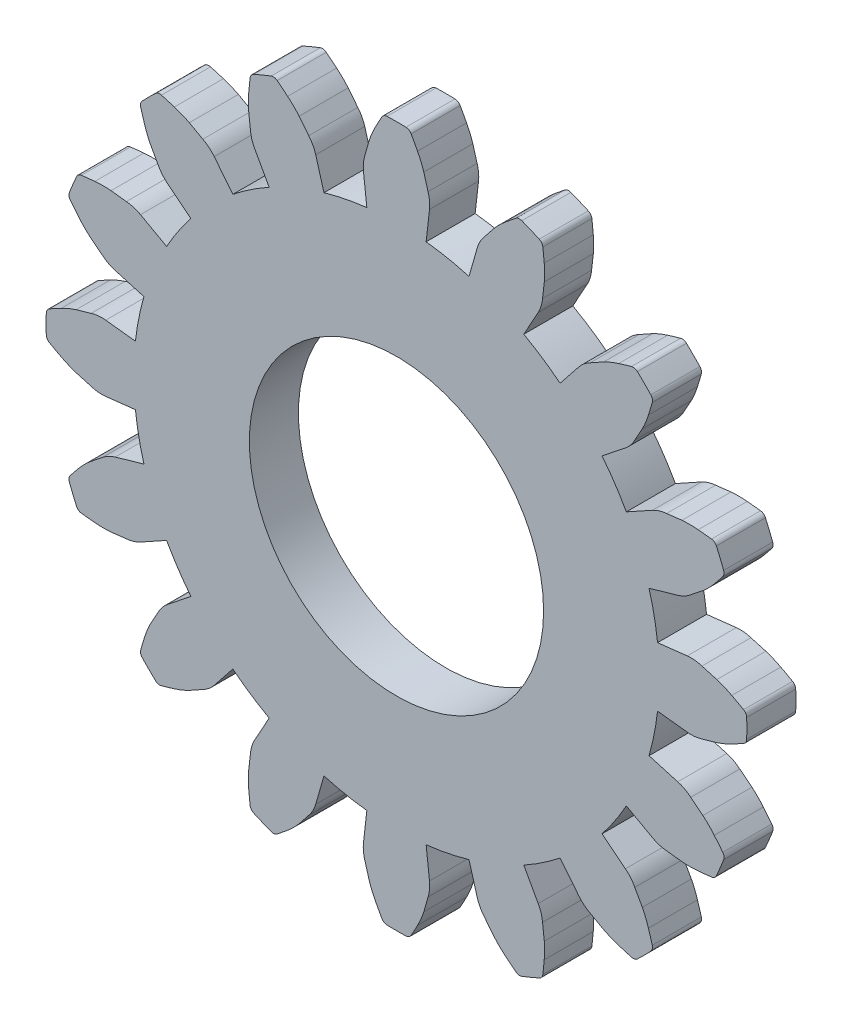
SolidWorks part; units mm, degrees
ref_plane "Front Plane" through (0, 0, 0) normal (0, 0, 1) x (1, 0, 0)
ref_plane "Top Plane" through (0, 0, 0) normal (0, 1, 0) x (1, 0, 0)
ref_plane "Right Plane" through (0, 0, 0) normal (1, 0, 0) x (0, 0, -1)
sketch "Model" plane through (0, 0, 0) normal (0, 0, 1) x (1, 0, 0)
  line L0 (26.7827, 18.0118) -> (27.9934, 18.1493)
  line L1 (26.7827, 15.5936) -> (27.9934, 15.4561)
  line L2 (26.435, 13.8453) -> (27.6061, 13.509)
  line L3 (25.5095, 11.6111) -> (26.5755, 11.0208)
  line L4 (24.5192, 10.129) -> (25.4725, 9.3701)
  line L5 (22.8092, 8.419) -> (23.5681, 7.4657)
  line L6 (21.3271, 7.4287) -> (21.9175, 6.3628)
  line L7 (19.0929, 6.5033) -> (19.4292, 5.3321)
  line L8 (17.3447, 6.1555) -> (17.4822, 4.9448)
  line L9 (14.9264, 6.1555) -> (14.7889, 4.9448)
  line L10 (13.1781, 6.5033) -> (12.8418, 5.3321)
  line L11 (10.9439, 7.4287) -> (10.3536, 6.3628)
  line L12 (9.4618, 8.419) -> (8.703, 7.4657)
  line L13 (7.7518, 10.129) -> (6.7985, 9.3701)
  line L14 (6.7615, 11.6111) -> (5.6956, 11.0208)
  line L15 (5.8361, 13.8453) -> (4.665, 13.509)
  line L16 (5.4883, 15.5936) -> (4.2777, 15.4561)
  line L17 (5.4883, 18.0118) -> (4.2777, 18.1493)
  line L18 (5.8361, 19.7601) -> (4.665, 20.0964)
  line L19 (6.7615, 21.9943) -> (5.6956, 22.5846)
  line L20 (7.7518, 23.4764) -> (6.7985, 24.2353)
  line L21 (9.4618, 25.1864) -> (8.703, 26.1397)
  line L22 (10.9439, 26.1767) -> (10.3536, 27.2426)
  line L23 (13.1781, 27.1021) -> (12.8418, 28.2733)
  line L24 (14.9264, 27.4499) -> (14.7889, 28.6606)
  line L25 (17.3447, 27.4499) -> (17.4822, 28.6606)
  line L26 (19.0929, 27.1021) -> (19.4292, 28.2733)
  line L27 (21.3271, 26.1767) -> (21.9175, 27.2426)
  line L28 (22.8092, 25.1864) -> (23.5681, 26.1397)
  line L29 (24.5192, 23.4764) -> (25.4725, 24.2353)
  line L30 (25.5095, 21.9943) -> (26.5755, 22.5846)
  line L31 (26.435, 19.7601) -> (27.6061, 20.0964)
  arc A0 (26.7827, 18.0118) -> (26.6453, 18.8932) centre (16.1355, 16.8027) ccw
  arc A1 (28.5916, 18.09) -> (27.9934, 18.1493) centre (28.1546, 16.7294) ccw
  arc A2 (29.1989, 17.9171) -> (28.5916, 18.09) centre (-551.5526, -2020.9533) ccw
  arc A3 (29.8078, 17.661) -> (29.1989, 17.9171) centre (28.0353, 14.2986) ccw
  arc A4 (30.2897, 17.4001) -> (29.8078, 17.661) centre (18.6277, -3.5692) ccw
  arc A5 (30.423, 16.8027) -> (30.4178, 17.189) centre (16.1355, 16.8027) ccw
  arc A6 (30.4178, 17.189) -> (30.2897, 17.4001) centre (30.1685, 17.1822) ccw
  arc A7 (26.6453, 14.7122) -> (26.7827, 15.5936) centre (16.1355, 16.8027) ccw
  arc A8 (27.9934, 15.4561) -> (28.5916, 15.5154) centre (28.1546, 16.876) ccw
  arc A9 (28.5916, 15.5154) -> (29.1989, 15.6883) centre (-551.5526, 2054.5587) ccw
  arc A10 (29.1989, 15.6883) -> (29.8078, 15.9444) centre (28.0353, 19.3068) ccw
  arc A11 (29.8078, 15.9444) -> (30.2897, 16.2052) centre (18.6277, 37.1746) ccw
  arc A12 (30.4178, 16.4164) -> (30.423, 16.8027) centre (16.1355, 16.8027) ccw
  arc A13 (30.2897, 16.2052) -> (30.4178, 16.4164) centre (30.1685, 16.4232) ccw
  arc A14 (26.435, 13.8453) -> (26.6453, 14.7122) centre (16.1355, 16.8027) ccw
  arc A15 (28.1361, 13.2252) -> (27.6061, 13.509) centre (27.2117, 12.1355) ccw
  arc A16 (28.631, 12.8332) -> (28.1361, 13.2252) centre (-1288.1554, -1648.5936) ccw
  arc A17 (29.0955, 12.3636) -> (28.631, 12.8332) centre (26.1712, 9.9353) ccw
  arc A18 (29.441, 11.9381) -> (29.0955, 12.3636) centre (10.642, -2.9722) ccw
  arc A19 (29.3355, 11.3351) -> (29.4785, 11.694) centre (16.1355, 16.8027) ccw
  arc A20 (29.4785, 11.694) -> (29.441, 11.9381) centre (29.2456, 11.7831) ccw
  arc A21 (25.0453, 10.8494) -> (25.5095, 11.6111) centre (16.1355, 16.8027) ccw
  arc A22 (26.5755, 11.0208) -> (27.1509, 10.8466) centre (27.2678, 12.2709) ccw
  arc A23 (27.1509, 10.8466) -> (27.778, 10.774) centre (271.4756, 2116.6886) ccw
  arc A24 (27.778, 10.774) -> (28.4386, 10.7776) centre (28.0878, 14.5623) ccw
  arc A25 (28.4386, 10.7776) -> (28.9837, 10.8341) centre (26.234, 34.6702) ccw
  arc A26 (29.1828, 10.9802) -> (29.3355, 11.3351) centre (16.1355, 16.8027) ccw
  arc A27 (28.9837, 10.8341) -> (29.1828, 10.9802) centre (28.9551, 11.0819) ccw
  arc A28 (24.5192, 10.129) -> (25.0453, 10.8494) centre (16.1355, 16.8027) ccw
  arc A29 (25.8536, 8.9051) -> (25.4725, 9.3701) centre (24.5825, 8.2521) ccw
  arc A30 (26.1607, 8.3535) -> (25.8536, 8.9051) centre (-1826.1917, -1022.6923) ccw
  arc A31 (26.4102, 7.7419) -> (26.1607, 8.3535) centre (22.7793, 6.6176) ccw
  arc A32 (26.5665, 7.2166) -> (26.4102, 7.7419) centre (3.4927, 0.6353) ccw
  arc A33 (26.2383, 6.6999) -> (26.5078, 6.9767) centre (16.1355, 16.8027) ccw
  arc A34 (26.5078, 6.9767) -> (26.5665, 7.2166) centre (26.3267, 7.1482) ccw
  arc A35 (22.0888, 7.893) -> (22.8092, 8.419) centre (16.1355, 16.8027) ccw
  arc A36 (23.5681, 7.4657) -> (24.0331, 7.0846) centre (24.6862, 8.3557) ccw
  arc A37 (24.0331, 7.0846) -> (24.5847, 6.7775) centre (1055.6305, 1859.1299) ccw
  arc A38 (24.5847, 6.7775) -> (25.1963, 6.528) centre (26.3206, 10.159) ccw
  arc A39 (25.1963, 6.528) -> (25.7216, 6.3717) centre (32.3029, 29.4456) ccw
  arc A40 (25.9615, 6.4305) -> (26.2383, 6.6999) centre (16.1355, 16.8027) ccw
  arc A41 (25.7216, 6.3717) -> (25.9615, 6.4305) centre (25.79, 6.6115) ccw
  arc A42 (21.3271, 7.4287) -> (22.0888, 7.893) centre (16.1355, 16.8027) ccw
  arc A43 (22.0916, 5.7874) -> (21.9175, 6.3628) centre (20.6673, 5.6704) ccw
  arc A44 (22.1643, 5.1602) -> (22.0916, 5.7874) centre (-2083.7504, -238.5374) ccw
  arc A45 (22.1607, 4.4997) -> (22.1643, 5.1602) centre (18.3759, 4.8504) ccw
  arc A46 (22.1041, 3.9545) -> (22.1607, 4.4997) centre (-1.7319, 6.7042) ccw
  arc A47 (21.6031, 3.6028) -> (21.958, 3.7554) centre (16.1355, 16.8027) ccw
  arc A48 (21.958, 3.7554) -> (22.1041, 3.9545) centre (21.8564, 3.9831) ccw
  arc A49 (18.226, 6.293) -> (19.0929, 6.5033) centre (16.1355, 16.8027) ccw
  arc A50 (19.4292, 5.3321) -> (19.713, 4.8021) centre (20.8028, 5.7265) ccw
  arc A51 (19.713, 4.8021) -> (20.1051, 4.3073) centre (1681.5318, 1321.0936) ccw
  arc A52 (20.1051, 4.3073) -> (20.5747, 3.8427) centre (23.0029, 6.767) ccw
  arc A53 (20.5747, 3.8427) -> (21.0001, 3.4973) centre (35.9105, 22.2962) ccw
  arc A54 (21.2443, 3.4598) -> (21.6031, 3.6028) centre (16.1355, 16.8027) ccw
  arc A55 (21.0001, 3.4973) -> (21.2443, 3.4598) centre (21.1551, 3.6926) ccw
  arc A56 (17.3447, 6.1555) -> (18.226, 6.293) centre (16.1355, 16.8027) ccw
  arc A57 (17.4228, 4.3466) -> (17.4822, 4.9448) centre (16.0622, 4.7836) ccw
  arc A58 (17.25, 3.7393) -> (17.4228, 4.3466) centre (-2021.6205, 584.4908) ccw
  arc A59 (16.9939, 3.1305) -> (17.25, 3.7393) centre (13.6314, 4.9029) ccw
  arc A60 (16.733, 2.6485) -> (16.9939, 3.1305) centre (-4.2364, 14.3105) ccw
  arc A61 (16.1355, 2.5152) -> (16.5218, 2.5204) centre (16.1355, 16.8027) ccw
  arc A62 (16.5218, 2.5204) -> (16.733, 2.6485) centre (16.5151, 2.7697) ccw
  arc A63 (14.045, 6.293) -> (14.9264, 6.1555) centre (16.1355, 16.8027) ccw
  arc A64 (14.7889, 4.9448) -> (14.8482, 4.3466) centre (16.2088, 4.7836) ccw
  arc A65 (14.8482, 4.3466) -> (15.0211, 3.7393) centre (2053.8916, 584.4908) ccw
  arc A66 (15.0211, 3.7393) -> (15.2772, 3.1305) centre (18.6397, 4.9029) ccw
  arc A67 (15.2772, 3.1305) -> (15.5381, 2.6485) centre (36.5075, 14.3105) ccw
  arc A68 (15.7493, 2.5204) -> (16.1355, 2.5152) centre (16.1355, 16.8027) ccw
  arc A69 (15.5381, 2.6485) -> (15.7493, 2.5204) centre (15.756, 2.7697) ccw
  arc A70 (13.1781, 6.5033) -> (14.045, 6.293) centre (16.1355, 16.8027) ccw
  arc A71 (12.5581, 4.8021) -> (12.8418, 5.3321) centre (11.4683, 5.7265) ccw
  arc A72 (12.166, 4.3073) -> (12.5581, 4.8021) centre (-1649.2607, 1321.0936) ccw
  arc A73 (11.6964, 3.8427) -> (12.166, 4.3073) centre (9.2682, 6.767) ccw
  arc A74 (11.2709, 3.4973) -> (11.6964, 3.8427) centre (-3.6394, 22.2962) ccw
  arc A75 (10.6679, 3.6028) -> (11.0268, 3.4598) centre (16.1355, 16.8027) ccw
  arc A76 (11.0268, 3.4598) -> (11.2709, 3.4973) centre (11.116, 3.6926) ccw
  arc A77 (10.1823, 7.893) -> (10.9439, 7.4287) centre (16.1355, 16.8027) ccw
  arc A78 (10.3536, 6.3628) -> (10.1795, 5.7874) centre (11.6038, 5.6704) ccw
  arc A79 (10.1795, 5.7874) -> (10.1068, 5.1602) centre (2116.0215, -238.5374) ccw
  arc A80 (10.1068, 5.1602) -> (10.1104, 4.4997) centre (13.8952, 4.8504) ccw
  arc A81 (10.1104, 4.4997) -> (10.167, 3.9545) centre (34.003, 6.7042) ccw
  arc A82 (10.3131, 3.7554) -> (10.6679, 3.6028) centre (16.1355, 16.8027) ccw
  arc A83 (10.167, 3.9545) -> (10.3131, 3.7554) centre (10.4147, 3.9831) ccw
  arc A84 (9.4618, 8.419) -> (10.1823, 7.893) centre (16.1355, 16.8027) ccw
  arc A85 (8.238, 7.0846) -> (8.703, 7.4657) centre (7.5849, 8.3557) ccw
  arc A86 (7.6864, 6.7775) -> (8.238, 7.0846) centre (-1023.3595, 1859.1299) ccw
  arc A87 (7.0747, 6.528) -> (7.6864, 6.7775) centre (5.9504, 10.159) ccw
  arc A88 (6.5495, 6.3717) -> (7.0747, 6.528) centre (-0.0318, 29.4456) ccw
  arc A89 (6.0327, 6.6999) -> (6.3096, 6.4305) centre (16.1355, 16.8027) ccw
  arc A90 (6.3096, 6.4305) -> (6.5495, 6.3717) centre (6.4811, 6.6115) ccw
  arc A91 (7.2258, 10.8494) -> (7.7518, 10.129) centre (16.1355, 16.8027) ccw
  arc A92 (6.7985, 9.3701) -> (6.4175, 8.9051) centre (7.6886, 8.2521) ccw
  arc A93 (6.4175, 8.9051) -> (6.1103, 8.3535) centre (1858.4628, -1022.6923) ccw
  arc A94 (6.1103, 8.3535) -> (5.8609, 7.7419) centre (9.4918, 6.6176) ccw
  arc A95 (5.8609, 7.7419) -> (5.7045, 7.2166) centre (28.7784, 0.6353) ccw
  arc A96 (5.7633, 6.9767) -> (6.0327, 6.6999) centre (16.1355, 16.8027) ccw
  arc A97 (5.7045, 7.2166) -> (5.7633, 6.9767) centre (5.9443, 7.1482) ccw
  arc A98 (6.7615, 11.6111) -> (7.2258, 10.8494) centre (16.1355, 16.8027) ccw
  arc A99 (5.1202, 10.8466) -> (5.6956, 11.0208) centre (5.0033, 12.2709) ccw
  arc A100 (4.493, 10.774) -> (5.1202, 10.8466) centre (-239.2045, 2116.6886) ccw
  arc A101 (3.8325, 10.7776) -> (4.493, 10.774) centre (4.1833, 14.5623) ccw
  arc A102 (3.2874, 10.8341) -> (3.8325, 10.7776) centre (6.0371, 34.6702) ccw
  arc A103 (2.9356, 11.3351) -> (3.0882, 10.9802) centre (16.1355, 16.8027) ccw
  arc A104 (3.0882, 10.9802) -> (3.2874, 10.8341) centre (3.316, 11.0819) ccw
  arc A105 (5.6258, 14.7122) -> (5.8361, 13.8453) centre (16.1355, 16.8027) ccw
  arc A106 (4.665, 13.509) -> (4.135, 13.2252) centre (5.0594, 12.1355) ccw
  arc A107 (4.135, 13.2252) -> (3.6401, 12.8332) centre (1320.4264, -1648.5936) ccw
  arc A108 (3.6401, 12.8332) -> (3.1756, 12.3636) centre (6.0998, 9.9353) ccw
  arc A109 (3.1756, 12.3636) -> (2.8301, 11.9381) centre (21.629, -2.9722) ccw
  arc A110 (2.7926, 11.694) -> (2.9356, 11.3351) centre (16.1355, 16.8027) ccw
  arc A111 (2.8301, 11.9381) -> (2.7926, 11.694) centre (3.0255, 11.7831) ccw
  arc A112 (5.4883, 15.5936) -> (5.6258, 14.7122) centre (16.1355, 16.8027) ccw
  arc A113 (3.6794, 15.5154) -> (4.2777, 15.4561) centre (4.1164, 16.876) ccw
  arc A114 (3.0722, 15.6883) -> (3.6794, 15.5154) centre (583.8237, 2054.5587) ccw
  arc A115 (2.4633, 15.9444) -> (3.0722, 15.6883) centre (4.2357, 19.3068) ccw
  arc A116 (1.9813, 16.2052) -> (2.4633, 15.9444) centre (13.6433, 37.1746) ccw
  arc A117 (1.848, 16.8027) -> (1.8533, 16.4164) centre (16.1355, 16.8027) ccw
  arc A118 (1.8533, 16.4164) -> (1.9813, 16.2052) centre (2.1025, 16.4232) ccw
  arc A119 (5.6258, 18.8932) -> (5.4883, 18.0118) centre (16.1355, 16.8027) ccw
  arc A120 (4.2777, 18.1493) -> (3.6794, 18.09) centre (4.1164, 16.7294) ccw
  arc A121 (3.6794, 18.09) -> (3.0722, 17.9171) centre (583.8237, -2020.9533) ccw
  arc A122 (3.0722, 17.9171) -> (2.4633, 17.661) centre (4.2357, 14.2986) ccw
  arc A123 (2.4633, 17.661) -> (1.9813, 17.4001) centre (13.6433, -3.5692) ccw
  arc A124 (1.8533, 17.189) -> (1.848, 16.8027) centre (16.1355, 16.8027) ccw
  arc A125 (1.9813, 17.4001) -> (1.8533, 17.189) centre (2.1025, 17.1822) ccw
  arc A126 (5.8361, 19.7601) -> (5.6258, 18.8932) centre (16.1355, 16.8027) ccw
  arc A127 (4.135, 20.3801) -> (4.665, 20.0964) centre (5.0594, 21.4699) ccw
  arc A128 (3.6401, 20.7722) -> (4.135, 20.3801) centre (1320.4264, 1682.1989) ccw
  arc A129 (3.1756, 21.2418) -> (3.6401, 20.7722) centre (6.0998, 23.6701) ccw
  arc A130 (2.8301, 21.6673) -> (3.1756, 21.2418) centre (21.629, 36.5776) ccw
  arc A131 (2.9356, 22.2703) -> (2.7926, 21.9114) centre (16.1355, 16.8027) ccw
  arc A132 (2.7926, 21.9114) -> (2.8301, 21.6673) centre (3.0255, 21.8223) ccw
  arc A133 (7.2258, 22.756) -> (6.7615, 21.9943) centre (16.1355, 16.8027) ccw
  arc A134 (5.6956, 22.5846) -> (5.1202, 22.7587) centre (5.0033, 21.3345) ccw
  arc A135 (5.1202, 22.7587) -> (4.493, 22.8314) centre (-239.2045, -2083.0832) ccw
  arc A136 (4.493, 22.8314) -> (3.8325, 22.8278) centre (4.1833, 19.043) ccw
  arc A137 (3.8325, 22.8278) -> (3.2874, 22.7712) centre (6.0371, -1.0648) ccw
  arc A138 (3.0882, 22.6251) -> (2.9356, 22.2703) centre (16.1355, 16.8027) ccw
  arc A139 (3.2874, 22.7712) -> (3.0882, 22.6251) centre (3.316, 22.5235) ccw
  arc A140 (7.7518, 23.4764) -> (7.2258, 22.756) centre (16.1355, 16.8027) ccw
  arc A141 (6.4175, 24.7002) -> (6.7985, 24.2353) centre (7.6886, 25.3533) ccw
  arc A142 (6.1103, 25.2519) -> (6.4175, 24.7002) centre (1858.4628, 1056.2977) ccw
  arc A143 (5.8609, 25.8635) -> (6.1103, 25.2519) centre (9.4918, 26.9878) ccw
  arc A144 (5.7045, 26.3888) -> (5.8609, 25.8635) centre (28.7784, 32.9701) ccw
  arc A145 (6.0327, 26.9055) -> (5.7633, 26.6287) centre (16.1355, 16.8027) ccw
  arc A146 (5.7633, 26.6287) -> (5.7045, 26.3888) centre (5.9443, 26.4572) ccw
  arc A147 (10.1823, 25.7124) -> (9.4618, 25.1864) centre (16.1355, 16.8027) ccw
  arc A148 (8.703, 26.1397) -> (8.238, 26.5207) centre (7.5849, 25.2496) ccw
  arc A149 (8.238, 26.5207) -> (7.6864, 26.8279) centre (-1023.3595, -1825.5245) ccw
  arc A150 (7.6864, 26.8279) -> (7.0747, 27.0774) centre (5.9504, 23.4464) ccw
  arc A151 (7.0747, 27.0774) -> (6.5495, 27.2337) centre (-0.0318, 4.1598) ccw
  arc A152 (6.3096, 27.1749) -> (6.0327, 26.9055) centre (16.1355, 16.8027) ccw
  arc A153 (6.5495, 27.2337) -> (6.3096, 27.1749) centre (6.4811, 26.9939) ccw
  arc A154 (10.9439, 26.1767) -> (10.1823, 25.7124) centre (16.1355, 16.8027) ccw
  arc A155 (10.1795, 27.818) -> (10.3536, 27.2426) centre (11.6038, 27.9349) ccw
  arc A156 (10.1068, 28.4452) -> (10.1795, 27.818) centre (2116.0215, 272.1427) ccw
  arc A157 (10.1104, 29.1057) -> (10.1068, 28.4452) centre (13.8952, 28.755) ccw
  arc A158 (10.167, 29.6508) -> (10.1104, 29.1057) centre (34.003, 26.9012) ccw
  arc A159 (10.6679, 30.0026) -> (10.3131, 29.85) centre (16.1355, 16.8027) ccw
  arc A160 (10.3131, 29.85) -> (10.167, 29.6508) centre (10.4147, 29.6223) ccw
  arc A161 (14.045, 27.3124) -> (13.1781, 27.1021) centre (16.1355, 16.8027) ccw
  arc A162 (12.8418, 28.2733) -> (12.5581, 28.8033) centre (11.4683, 27.8788) ccw
  arc A163 (12.5581, 28.8033) -> (12.166, 29.2981) centre (-1649.2607, -1287.4882) ccw
  arc A164 (12.166, 29.2981) -> (11.6964, 29.7627) centre (9.2682, 26.8384) ccw
  arc A165 (11.6964, 29.7627) -> (11.2709, 30.1081) centre (-3.6394, 11.3092) ccw
  arc A166 (11.0268, 30.1456) -> (10.6679, 30.0026) centre (16.1355, 16.8027) ccw
  arc A167 (11.2709, 30.1081) -> (11.0268, 30.1456) centre (11.116, 29.9127) ccw
  arc A168 (14.9264, 27.4499) -> (14.045, 27.3124) centre (16.1355, 16.8027) ccw
  arc A169 (14.8482, 29.2588) -> (14.7889, 28.6606) centre (16.2088, 28.8218) ccw
  arc A170 (15.0211, 29.866) -> (14.8482, 29.2588) centre (2053.8916, -550.8854) ccw
  arc A171 (15.2772, 30.4749) -> (15.0211, 29.866) centre (18.6397, 28.7025) ccw
  arc A172 (15.5381, 30.9569) -> (15.2772, 30.4749) centre (36.5075, 19.2949) ccw
  arc A173 (16.1355, 31.0902) -> (15.7493, 31.085) centre (16.1355, 16.8027) ccw
  arc A174 (15.7493, 31.085) -> (15.5381, 30.9569) centre (15.756, 30.8357) ccw
  arc A175 (18.226, 27.3124) -> (17.3447, 27.4499) centre (16.1355, 16.8027) ccw
  arc A176 (17.4822, 28.6606) -> (17.4228, 29.2588) centre (16.0622, 28.8218) ccw
  arc A177 (17.4228, 29.2588) -> (17.25, 29.866) centre (-2021.6205, -550.8854) ccw
  arc A178 (17.25, 29.866) -> (16.9939, 30.4749) centre (13.6314, 28.7025) ccw
  arc A179 (16.9939, 30.4749) -> (16.733, 30.9569) centre (-4.2364, 19.2949) ccw
  arc A180 (16.5218, 31.085) -> (16.1355, 31.0902) centre (16.1355, 16.8027) ccw
  arc A181 (16.733, 30.9569) -> (16.5218, 31.085) centre (16.5151, 30.8357) ccw
  arc A182 (19.0929, 27.1021) -> (18.226, 27.3124) centre (16.1355, 16.8027) ccw
  arc A183 (19.713, 28.8033) -> (19.4292, 28.2733) centre (20.8028, 27.8788) ccw
  arc A184 (20.1051, 29.2981) -> (19.713, 28.8033) centre (1681.5318, -1287.4882) ccw
  arc A185 (20.5747, 29.7627) -> (20.1051, 29.2981) centre (23.0029, 26.8384) ccw
  arc A186 (21.0001, 30.1081) -> (20.5747, 29.7627) centre (35.9105, 11.3092) ccw
  arc A187 (21.6031, 30.0026) -> (21.2443, 30.1456) centre (16.1355, 16.8027) ccw
  arc A188 (21.2443, 30.1456) -> (21.0001, 30.1081) centre (21.1551, 29.9127) ccw
  arc A189 (22.0888, 25.7124) -> (21.3271, 26.1767) centre (16.1355, 16.8027) ccw
  arc A190 (21.9175, 27.2426) -> (22.0916, 27.818) centre (20.6673, 27.9349) ccw
  arc A191 (22.0916, 27.818) -> (22.1643, 28.4452) centre (-2083.7504, 272.1427) ccw
  arc A192 (22.1643, 28.4452) -> (22.1607, 29.1057) centre (18.3759, 28.755) ccw
  arc A193 (22.1607, 29.1057) -> (22.1041, 29.6508) centre (-1.7319, 26.9012) ccw
  arc A194 (21.958, 29.85) -> (21.6031, 30.0026) centre (16.1355, 16.8027) ccw
  arc A195 (22.1041, 29.6508) -> (21.958, 29.85) centre (21.8564, 29.6223) ccw
  arc A196 (22.8092, 25.1864) -> (22.0888, 25.7124) centre (16.1355, 16.8027) ccw
  arc A197 (24.0331, 26.5207) -> (23.5681, 26.1397) centre (24.6862, 25.2496) ccw
  arc A198 (24.5847, 26.8279) -> (24.0331, 26.5207) centre (1055.6305, -1825.5245) ccw
  arc A199 (25.1963, 27.0774) -> (24.5847, 26.8279) centre (26.3206, 23.4464) ccw
  arc A200 (25.7216, 27.2337) -> (25.1963, 27.0774) centre (32.3029, 4.1598) ccw
  arc A201 (26.2383, 26.9055) -> (25.9615, 27.1749) centre (16.1355, 16.8027) ccw
  arc A202 (25.9615, 27.1749) -> (25.7216, 27.2337) centre (25.79, 26.9939) ccw
  arc A203 (25.0453, 22.756) -> (24.5192, 23.4764) centre (16.1355, 16.8027) ccw
  arc A204 (25.4725, 24.2353) -> (25.8536, 24.7002) centre (24.5825, 25.3533) ccw
  arc A205 (25.8536, 24.7002) -> (26.1607, 25.2519) centre (-1826.1917, 1056.2977) ccw
  arc A206 (26.1607, 25.2519) -> (26.4102, 25.8635) centre (22.7793, 26.9878) ccw
  arc A207 (26.4102, 25.8635) -> (26.5665, 26.3888) centre (3.4927, 32.9701) ccw
  arc A208 (26.5078, 26.6287) -> (26.2383, 26.9055) centre (16.1355, 16.8027) ccw
  arc A209 (26.5665, 26.3888) -> (26.5078, 26.6287) centre (26.3267, 26.4572) ccw
  arc A210 (25.5095, 21.9943) -> (25.0453, 22.756) centre (16.1355, 16.8027) ccw
  arc A211 (27.1509, 22.7587) -> (26.5755, 22.5846) centre (27.2678, 21.3345) ccw
  arc A212 (27.778, 22.8314) -> (27.1509, 22.7587) centre (271.4756, -2083.0832) ccw
  arc A213 (28.4386, 22.8278) -> (27.778, 22.8314) centre (28.0878, 19.043) ccw
  arc A214 (28.9837, 22.7712) -> (28.4386, 22.8278) centre (26.234, -1.0648) ccw
  arc A215 (29.3355, 22.2703) -> (29.1828, 22.6251) centre (16.1355, 16.8027) ccw
  arc A216 (29.1828, 22.6251) -> (28.9837, 22.7712) centre (28.9551, 22.5235) ccw
  arc A217 (26.6453, 18.8932) -> (26.435, 19.7601) centre (16.1355, 16.8027) ccw
  arc A218 (27.6061, 20.0964) -> (28.1361, 20.3801) centre (27.2117, 21.4699) ccw
  arc A219 (28.1361, 20.3801) -> (28.631, 20.7722) centre (-1288.1554, 1682.1989) ccw
  arc A220 (28.631, 20.7722) -> (29.0955, 21.2418) centre (26.1712, 23.6701) ccw
  arc A221 (29.0955, 21.2418) -> (29.441, 21.6673) centre (10.642, 36.5776) ccw
  arc A222 (29.4785, 21.9114) -> (29.3355, 22.2703) centre (16.1355, 16.8027) ccw
  arc A223 (29.441, 21.6673) -> (29.4785, 21.9114) centre (29.2456, 21.8223) ccw
  circle A224 centre (16.1355, 16.8027) radius 6
  dimension "D1" = 12
extrude "Boss-Extrude1" add sketch "Model" along normal blind 2
